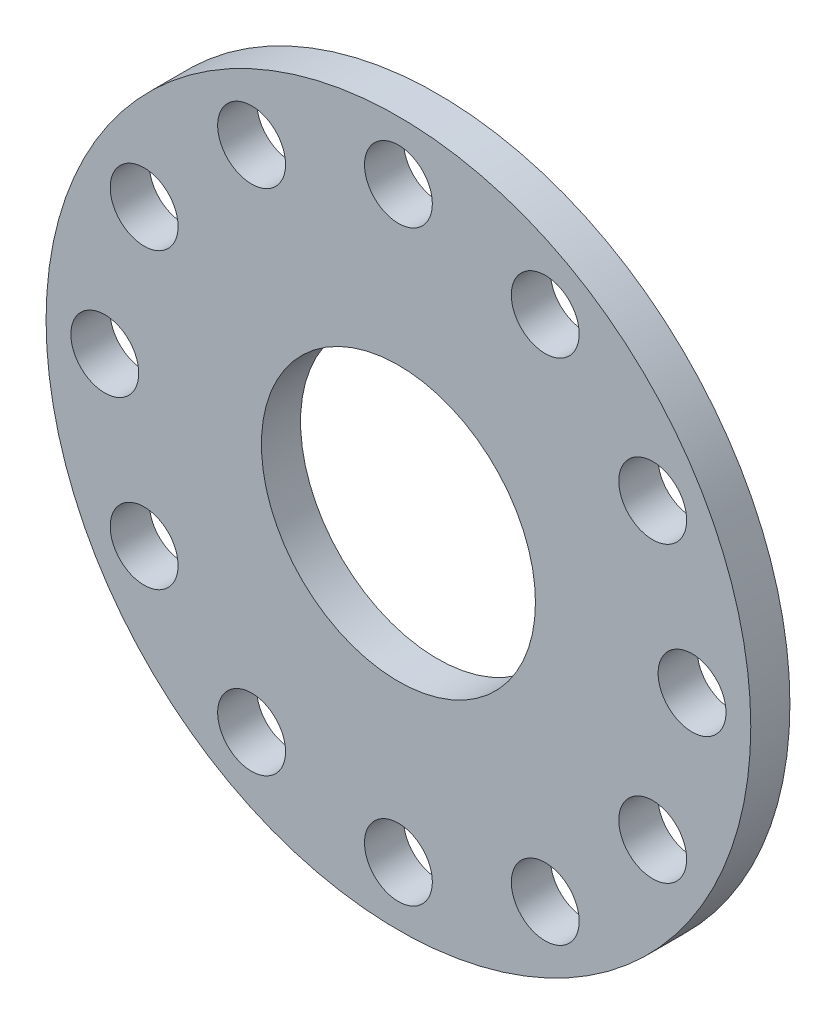
SolidWorks part; units mm, degrees
material "Thornel Mat VMA"
ref_plane "前视基准面" through (0, 0, 0) normal (0, 0, 1) x (1, 0, 0)
ref_plane "上视基准面" through (0, 0, 0) normal (0, 1, 0) x (1, 0, 0)
ref_plane "右视基准面" through (0, 0, 0) normal (1, 0, 0) x (0, 0, -1)
sketch "草图1" plane through (0, 0, 0) normal (0, 0, 1) x (1, 0, 0)
  line L0 (0, 0) -> (0, 22.5) construction
  line L1 (0, 0) -> (19.4856, 11.25) construction
  circle A0 centre (0, 0) radius 27
  circle A1 centre (0, 0) radius 10.5
  circle A2 centre (0, 0) radius 22.5 construction
  circle A3 centre (0, 22.5) radius 2.6
  circle A4 centre (19.4856, 11.25) radius 2.6
  circle A5 centre (19.4856, -11.25) radius 2.6
  circle A6 centre (0, -22.5) radius 2.6
  circle A7 centre (-19.4856, -11.25) radius 2.6
  circle A8 centre (-19.4856, 11.25) radius 2.6
  dimension "D1" = 54
  dimension "D2" = 21
  dimension "D3" = 45
  dimension "D4" = 5.2
  dimension "D6" = 60
  dimension "D5" = 6
extrude "凸台-拉伸1" add sketch "草图1" along normal blind 3
sketch "草图3" plane through (0, 0, 3) normal (0, 0, 1) x (1, 0, 0)
  line L0 (0, 22.5) -> (0, 0) construction
  line L1 (0, 0) -> (19.4856, 11.25) construction
  line L2 (11.25, 19.4856) -> (0, 0) construction
  line L3 (0, 0) -> (11.25, 19.4856) construction
  line L4 (0, 0) -> (22.5, 0) construction
  circle A0 centre (0, 0) radius 22.5 construction
  circle A1 centre (11.25, 19.4856) radius 2.6
  circle A2 centre (0, 22.5) radius 2.6 construction
  circle A3 centre (22.5, 0) radius 2.6
  circle A4 centre (11.25, -19.4856) radius 2.6
  circle A5 centre (-11.25, -19.4856) radius 2.6
  circle A6 centre (-22.5, 0) radius 2.6
  circle A7 centre (-11.25, 19.4856) radius 2.6
  dimension "D1" = 30
  dimension "D3" = 60
  dimension "D2" = 6
extrude "切除-拉伸2" cut sketch "草图3" against normal blind 3
